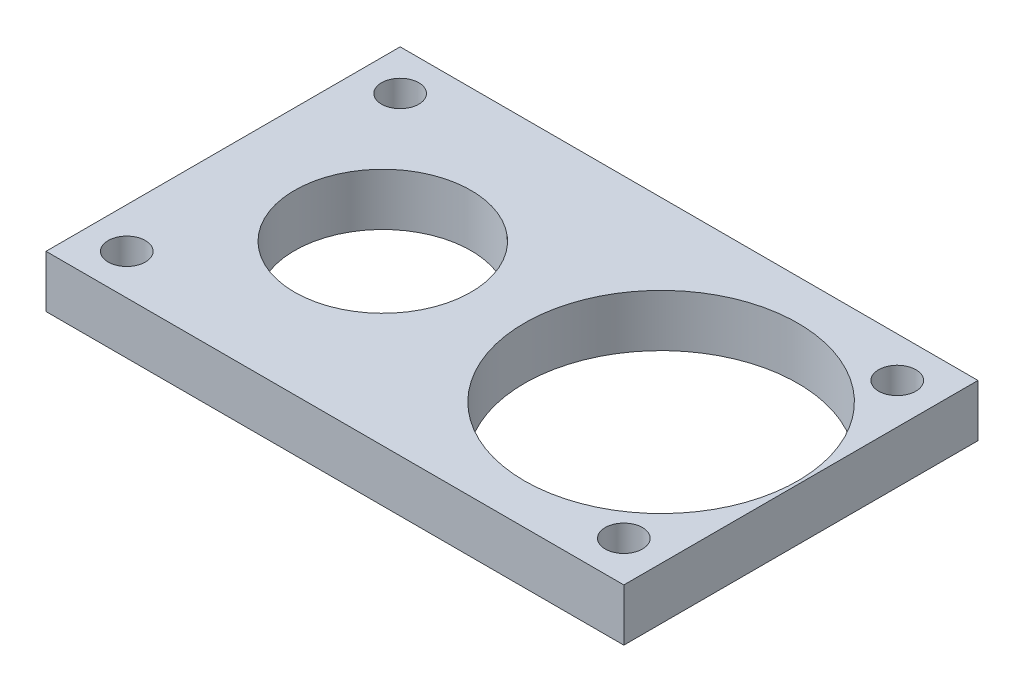
SolidWorks part; units mm, degrees
ref_plane "Front Plane" through (0, 0, 0) normal (0, 0, 1) x (1, 0, 0)
ref_plane "Top Plane" through (0, 0, 0) normal (0, 1, 0) x (1, 0, 0)
ref_plane "Right Plane" through (0, 0, 0) normal (1, 0, 0) x (0, 0, -1)
sketch "Sketch11" plane through (0, 0, 0) normal (0, 1, 0) x (1, 0, 0)
  line L0 (-25.6, 11) -> (14.4, 11) construction
  line L1 (-28.85, 14.25) -> (17.65, 14.25)
  line L2 (-28.85, 14.25) -> (-28.85, -14.25)
  line L3 (-28.85, -14.25) -> (17.65, -14.25)
  line L4 (17.65, 14.25) -> (17.65, -14.25)
  line L5 (14.4, 11) -> (14.4, -11) construction
  circle A0 centre (6.4, 0) radius 14.4 construction
  circle A1 centre (-16, 0) radius 8 construction
  circle A3 centre (0, 0) radius 8 construction
  circle A4 centre (6.4, 0) radius 3 construction
  circle A5 centre (-25.6, 11) radius 1.5
  circle A6 centre (14.4, 11) radius 1.5
  circle A7 centre (14.4, -11) radius 1.5
  circle A8 centre (-25.6, -11) radius 1.5
  point P4 (-28.85, 0)
  point P21 (-5.6, 11)
  point P22 (-5.6, 14.25)
  point P23 (14.4, 0)
  point P24 (17.65, 0)
  dimension "D3" = 28.8
  dimension "D5" = 16
  dimension "D6" = 6
  dimension "D9" = 3
  dimension "D1" = 46.5
  dimension "D2" = 28.5
  dimension "D4" = 11.25
  dimension "D7" = 40
  dimension "D8" = 22
extrude "Boss-Extrude3" add sketch "Sketch11" against normal blind 4.2
sketch "Sketch12" plane through (0, 0, 0) normal (0, 1, 0) x (1, 0, 0)
  circle A0 centre (6.4, 0) radius 11
  dimension "D1" = 22
  dimension "D2" = 6.4
extrude "Cut-Extrude6" cut sketch "Sketch12" against normal through all
sketch "Sketch13" plane through (0, 0, 0) normal (0, 1, 0) x (1, 0, 0)
  circle A0 centre (-16, 0) radius 7.1
  dimension "D2" = 14.2
  dimension "D1" = 16
extrude "Cut-Extrude7" cut sketch "Sketch13" against normal through all
equation "\"drive_gear_pitch_diameter\"= 0.8mm * \"drive_gear_tooth_count\""
equation "\"driven_gear_pitch_diameter\"= 0.8mm * \"driven_gear_tooth_count\""
equation "\"drive_gear_tooth_count\"= 36"
equation "\"driven_gear_tooth_count\"= 20"
equation "\"plastic_shell_thickness\"= 3mm"
equation "\"servo_horn_distance_to_center\"= ( \"drive_gear_pitch_diameter\" / 2 ) - ( \"driven_gear_pitch_diameter\" / 2 )"
equation "\"D3@Sketch11\"=\"drive_gear_pitch_diameter\""
equation "\"D5@Sketch11\"=\"driven_gear_pitch_diameter\""
equation "\"D2@Sketch12\"=\"servo_horn_distance_to_center\""
equation "\"D1@Sketch13\"=\"driven_gear_pitch_diameter\""
